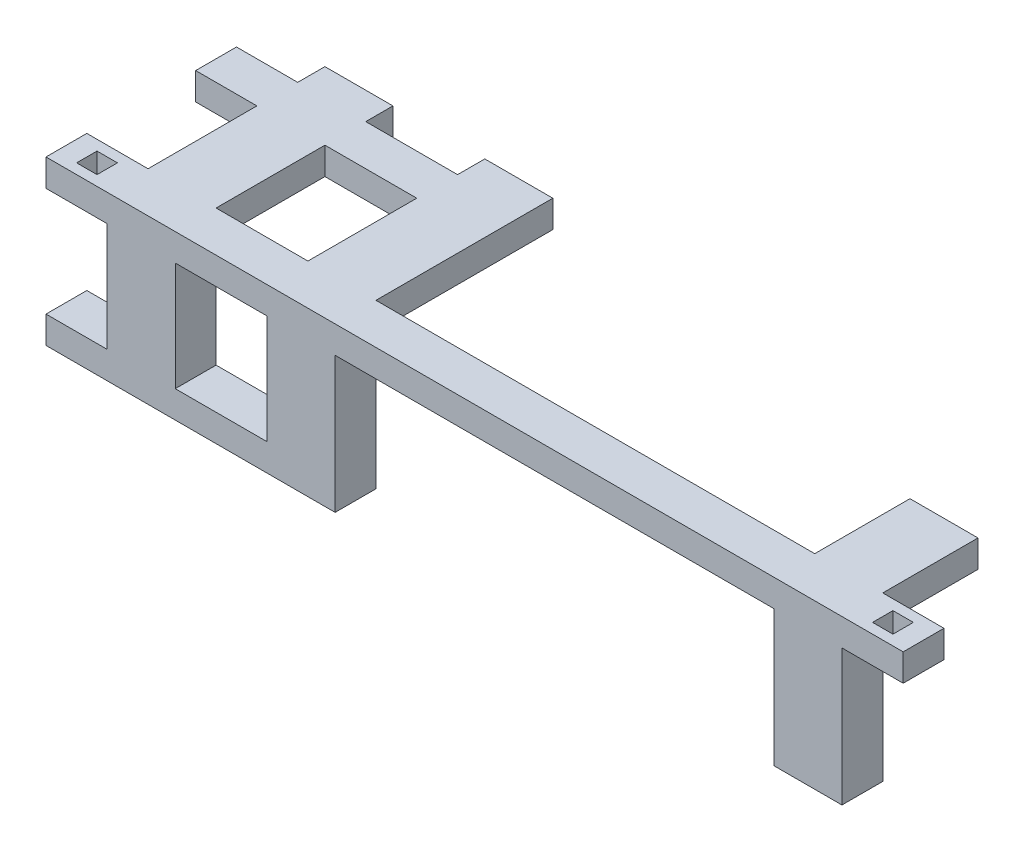
SolidWorks part; units mm, degrees
ref_plane "Front Plane" through (0, 0, 0) normal (0, 0, 1) x (1, 0, 0)
ref_plane "Top Plane" through (0, 0, 0) normal (0, 1, 0) x (1, 0, 0)
ref_plane "Right Plane" through (0, 0, 0) normal (1, 0, 0) x (0, 0, -1)
sketch "Sketch1" plane through (0, 0, 0) normal (0, 1, 0) x (1, 0, 0)
  line L1 (0, 0) -> (126, 0)
  line L2 (0, 0) -> (0, 6)
  line L3 (0, 6) -> (126, 6)
  line L4 (126, 0) -> (126, 6)
  dimension "D1" = 126
  dimension "D2" = 6
extrude "Boss-Extrude1" add sketch "Sketch1" along normal blind 4
sketch "Sketch2" plane through (0, 4, 0) normal (0, 1, 0) x (1, 0, 0)
  line L0 (126, 6) -> (0, 6) construction
  line L1 (120, 4.5) -> (123, 4.5)
  line L2 (120, 4.5) -> (120, 1.5)
  line L3 (120, 1.5) -> (123, 1.5)
  line L4 (123, 4.5) -> (123, 1.5)
  line L5 (126, 0) -> (126, 6) construction
  line L6 (0, 6) -> (0, 0) construction
  line L7 (3, 4.5) -> (6, 4.5)
  line L8 (3, 4.5) -> (3, 1.5)
  line L9 (3, 1.5) -> (6, 1.5)
  line L10 (6, 4.5) -> (6, 1.5)
  dimension "D1" = 3
  dimension "D2" = 3
  dimension "D3" = 1.5
  dimension "D4" = 3
  dimension "D5" = 3
  dimension "D6" = 3
  dimension "D7" = 1.5
  dimension "D8" = 3
extrude "Cut-Extrude1" cut sketch "Sketch2" against normal blind 4
sketch "Sketch3" plane through (0, 0, 0) normal (0, 1, 0) x (1, 0, 0)
  line L0 (126, 6) -> (0, 6) construction
  line L1 (9, 6) -> (19, 6)
  line L2 (9, 6) -> (9, 0)
  line L3 (9, 0) -> (19, 0)
  line L4 (19, 6) -> (19, 0)
  line L5 (0, 0) -> (126, 0) construction
  line L6 (6, 1.5) -> (6, 4.5) construction
  line L7 (120, 4.5) -> (120, 1.5) construction
  line L8 (107, 6) -> (117, 6)
  line L9 (107, 6) -> (107, 0)
  line L10 (107, 0) -> (117, 0)
  line L11 (117, 6) -> (117, 0)
  line L13 (32.5, 6) -> (42.5, 6)
  line L14 (32.5, 6) -> (32.5, 0)
  line L15 (32.5, 0) -> (42.5, 0)
  line L16 (42.5, 6) -> (42.5, 0)
  dimension "D1" = 10
  dimension "D2" = 3
  dimension "D3" = 10
  dimension "D4" = 3
  dimension "D5" = 10
  dimension "D6" = 23.5
extrude "Boss-Extrude2" add sketch "Sketch3" against normal blind 20
sketch "Sketch4" plane through (0, 0, -6) normal (0, 0, -1) x (-1, 0, 0)
  line L0 (-126, 4) -> (0, 4) construction
  line L1 (-19, 0) -> (-9, 0)
  line L2 (-19, 0) -> (-19, 4)
  line L3 (-19, 4) -> (-9, 4)
  line L4 (-9, 0) -> (-9, 4)
  line L6 (-42.5, 0) -> (-32.5, 0)
  line L7 (-42.5, 0) -> (-42.5, 4)
  line L8 (-42.5, 4) -> (-32.5, 4)
  line L9 (-32.5, 0) -> (-32.5, 4)
  dimension "D1" = 10
  dimension "D2" = 10
extrude "Boss-Extrude3" add sketch "Sketch4" along normal blind 26
sketch "Sketch5" plane through (42.5, 0, 0) normal (1, 0, 0) x (0, 0, -1)
  line L0 (32, 4) -> (6, 4) construction
  line L1 (28, 4) -> (22, 4)
  line L2 (28, 4) -> (28, 0)
  line L3 (28, 0) -> (22, 0)
  line L4 (22, 4) -> (22, 0)
  line L5 (32, 0) -> (6, 0) construction
  line L6 (32, 4) -> (32, 0) construction
  line L7 (6, -20) -> (6, 0) construction
  line L8 (0, -20) -> (6, -20)
  line L9 (0, -20) -> (0, -16)
  line L10 (0, -16) -> (6, -16)
  line L11 (6, -20) -> (6, -16)
  dimension "D1" = 4
  dimension "D2" = 6
  dimension "D3" = 4
extrude "Boss-Extrude4" add sketch "Sketch5" against normal blind 42.5
sketch "Sketch6" plane through (0, 0, -6) normal (0, 0, -1) x (-1, 0, 0)
  line L0 (-126, 4) -> (-42.5, 4) construction
  line L1 (-117, 0) -> (-107, 0)
  line L2 (-117, 0) -> (-117, 4)
  line L3 (-117, 4) -> (-107, 4)
  line L4 (-107, 0) -> (-107, 4)
  dimension "D1" = 10
extrude "Boss-Extrude5" add sketch "Sketch6" along normal blind 14
